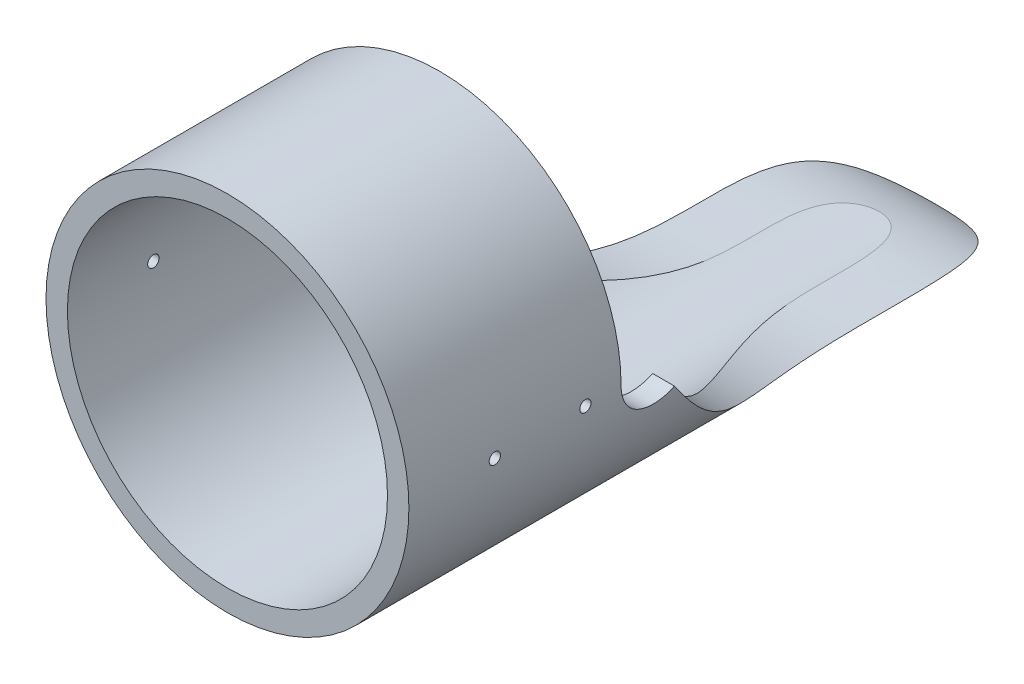
SolidWorks part; units mm, degrees
material "PVC Rigid"
ref_plane "Front Plane" through (0, 0, 0) normal (0, 0, 1) x (1, 0, 0)
ref_plane "Top Plane" through (0, 0, 0) normal (0, 1, 0) x (1, 0, 0)
ref_plane "Right Plane" through (0, 0, 0) normal (1, 0, 0) x (0, 0, -1)
sketch "Sketch1" plane through (0, 0, 0) normal (0, 0, 1) x (1, 0, 0)
  circle A0 centre (0, 0) radius 44.875
  circle A1 centre (0, 0) radius 50.875
  dimension "D1" = 89.75
  dimension "D2" = 6
extrude "Boss-Extrude1" add sketch "Sketch1" along normal blind 258
sketch "Sketch2" plane through (0, 0, 0) normal (1, 0, 0) x (0, 0, -1)
  line L0 (-198.5, -50.875) -> (0, -50.875)
  line L1 (-198.5, 50.875) -> (-198.5, -50.875)
  line L2 (-198.5, 50.875) -> (-139, 50.875)
  line L3 (0, 50.875) -> (-258, 50.875) construction
  line L4 (-129, 50.875) -> (-129, -50.875) construction
  line L5 (0, -50.875) -> (0, 50.875) construction
  line L8 (-139, 0) -> (-139, 50.875)
  arc A0 (-139, 0) -> (-123.3866, -8.2758) centre (-129, 0) ccw
  spline S0 degree 3 poles (-123.3866, -8.2758) (-81.7526, -64.6431) (-28.4139, -31.2131) (0, -50.875) knots 0.043569 0.043569 0.043569 0.043569 1 1 1 1
  dimension "D1" = 10
extrude "Cut-Extrude1" cut sketch "Sketch2" against normal through all and the other way through all flip side to cut
sketch "Sketch4" plane through (0, 0, 0) normal (1, 0, 0) x (0, 0, -1)
  circle A0 centre (-149, 0) radius 1.5875
  circle A1 centre (-174.4, 0) radius 1.5875
  dimension "D1" = 3.175
  dimension "D4" = 25.4
extrude "Cut-Extrude3" cut sketch "Sketch4" against normal through all and the other way through all
